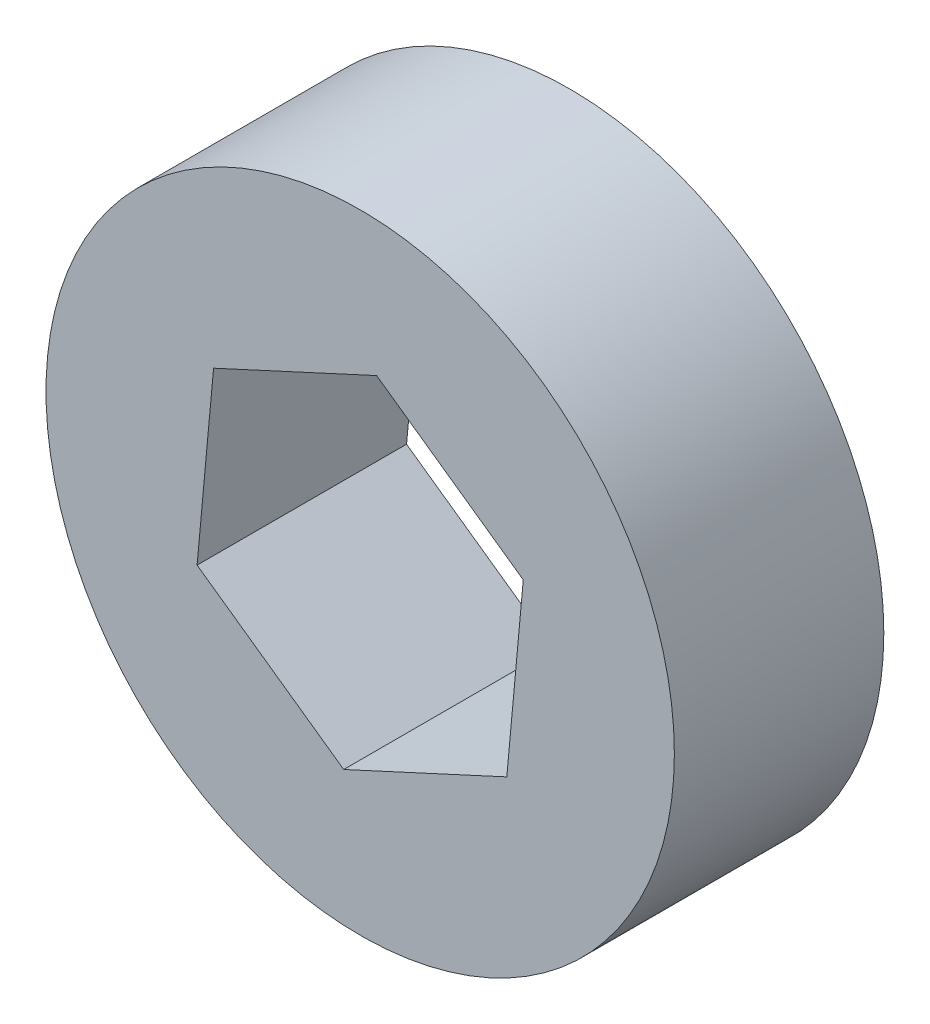
SolidWorks part; units mm, degrees
ref_plane "Plan de face" through (0, 0, 0) normal (0, 0, 1) x (1, 0, 0)
ref_plane "Plan de dessus" through (0, 0, 0) normal (0, 1, 0) x (1, 0, 0)
ref_plane "Plan de droite" through (0, 0, 0) normal (1, 0, 0) x (0, 0, -1)
sketch "Esquisse1" plane through (0, 0, 0) normal (0, 0, 1) x (1, 0, 0)
  line L1 (0.3932, 4.2685) -> (-3.5, 2.4747)
  line L2 (-3.5, 2.4747) -> (-3.8932, -1.7937)
  line L3 (-3.8932, -1.7937) -> (-0.3932, -4.2685)
  line L4 (-0.3932, -4.2685) -> (3.5, -2.4747)
  line L5 (3.5, -2.4747) -> (3.8932, 1.7937)
  line L6 (3.8932, 1.7937) -> (0.3932, 4.2685)
  circle A0 centre (0, 0) radius 7.5
  circle A1 centre (0, 0) radius 3.7122 construction
  dimension "D1" = 15
  dimension "D2" = 7
extrude "Boss.-Extru.1" add sketch "Esquisse1" along normal blind 5
